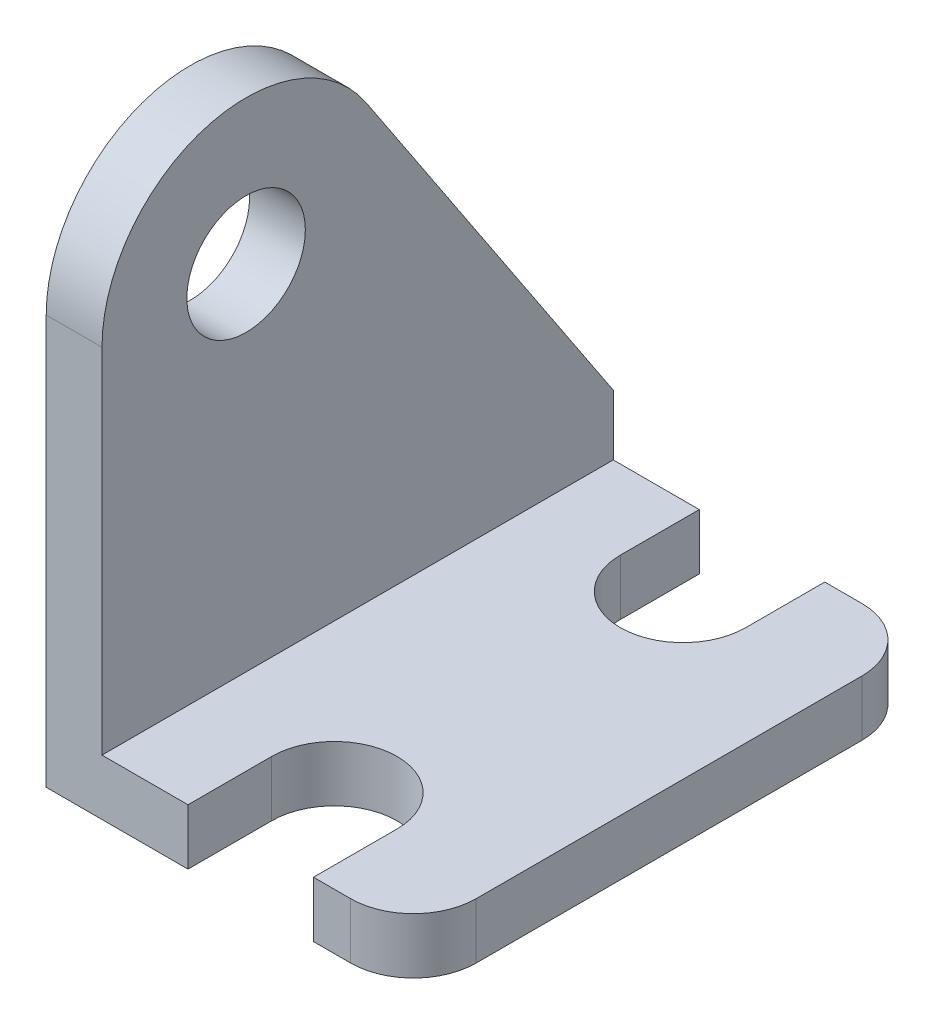
SolidWorks part; units mm, degrees
material "AISI 316 Annealed Stainless Steel Bar (SS)"
ref_plane "Front" through (0, 0, 0) normal (0, 0, 1) x (1, 0, 0)
ref_plane "Top" through (0, 0, 0) normal (0, 1, 0) x (1, 0, 0)
ref_plane "Right" through (0, 0, 0) normal (1, 0, 0) x (0, 0, -1)
sketch "Sketch2" plane through (0, 0, 0) normal (0, 1, 0) x (1, 0, 0)
  line L0 (0, 0) -> (60.4446, 0) construction
  line L1 (0, 13.97) -> (7.747, 13.97)
  line L2 (0, -13.97) -> (7.747, -13.97)
  line L3 (7.747, 13.97) -> (7.747, 9.652)
  line L4 (7.747, -13.97) -> (7.747, -9.398)
  line L5 (14.605, 9.652) -> (14.605, 13.97)
  line L6 (14.605, -9.398) -> (14.605, -13.97)
  line L7 (14.605, 13.97) -> (16.637, 13.97)
  line L8 (14.605, -13.97) -> (16.637, -13.97)
  line L9 (20.066, 10.541) -> (20.066, -10.541)
  line L10 (0, -13.97) -> (0, 13.97)
  arc A0 (16.637, 13.97) -> (20.066, 10.541) centre (16.637, 10.541) cw
  arc A1 (16.637, -13.97) -> (20.066, -10.541) centre (16.637, -10.541) ccw
  arc A2 (14.605, 9.652) -> (7.747, 9.652) centre (11.176, 9.652) cw
  arc A3 (14.605, -9.398) -> (7.747, -9.398) centre (11.176, -9.398) ccw
  dimension "D1" = 3.429
  dimension "J" = 27.94
  dimension "G or E" = 11.176
  dimension "H or F" = 20.066
  dimension "C or D" = 6.858
  dimension "A" = 19.05
  dimension "B Or J-A-B" = 4.318
extrude "Base-Extrude" add sketch "Sketch2" along normal blind 3.048
sketch "Sketch3" plane through (0, 0, 0) normal (-1, 0, 0) x (0, 0, 1)
  line L0 (-13.97, 0) -> (-13.97, 22.352)
  line L1 (0.4653, 26.7051) -> (13.97, 6.35)
  line L2 (13.97, 6.35) -> (13.97, 0)
  line L3 (13.97, 0) -> (-13.97, 0)
  line L4 (-13.97, 3.048) -> (-13.97, 0) construction
  line L6 (-13.97, 0) -> (13.97, 0) construction
  arc A0 (-13.97, 22.352) -> (0.4653, 26.7051) centre (-6.096, 22.352) cw
  circle A1 centre (-6.096, 22.352) radius 3.2385
  dimension "P" = 6.477
  dimension "N" = 7.874
  dimension "D2" = 6.35
  dimension "L" = 22.352
  dimension "J" = 27.94
extrude "FrontRib" [suppressed] add sketch "Sketch3" against normal blind 3.048
sketch "Sketch4" plane through (0, 0, 0) normal (-1, 0, 0) x (0, 0, 1)
  line L1 (10.541, 0) -> (-10.541, 0) construction
  line L3 (13.97, 3.048) -> (13.97, 0) construction
  line L4 (13.97, 22.352) -> (13.97, 0)
  line L6 (13.97, 0) -> (-13.97, 0)
  line L7 (-0.4653, 26.7051) -> (-13.97, 6.35)
  line L8 (-13.97, 0) -> (-13.97, 6.35)
  line L9 (-13.97, 3.048) -> (-13.97, 0) construction
  arc A4 (-0.4653, 26.7051) -> (13.97, 22.352) centre (6.096, 22.352) cw
  circle A5 centre (6.096, 22.352) radius 3.2385
  dimension "N" = 7.874
  dimension "P" = 6.477
  dimension "D4" = 6.35
  dimension "L" = 22.352
extrude "RearRib" add sketch "Sketch4" against normal blind 3.048
